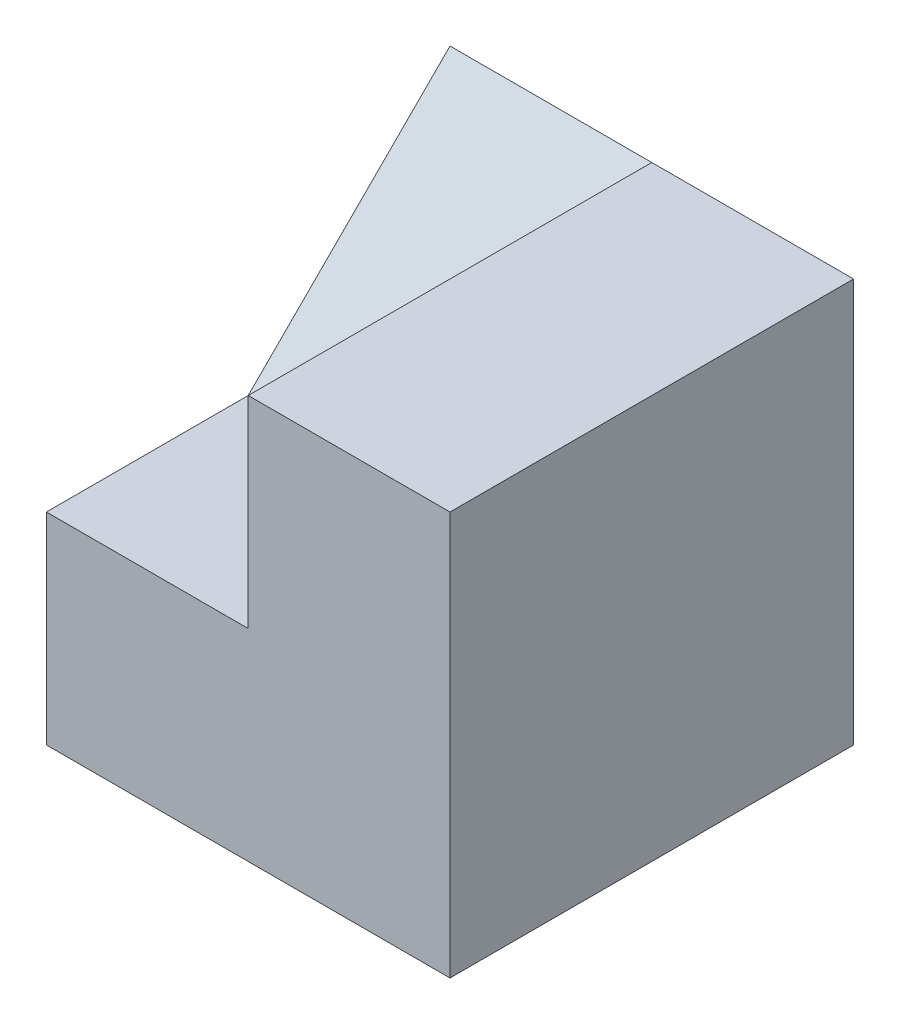
SolidWorks part; units mm, degrees
ref_plane "Front" through (0, 0, 0) normal (0, 0, 1) x (1, 0, 0)
ref_plane "Top" through (0, 0, 0) normal (0, 1, 0) x (1, 0, 0)
ref_plane "Right" through (0, 0, 0) normal (1, 0, 0) x (0, 0, -1)
sketch "Sketch1" plane through (0, 0, 0) normal (0, 1, 0) x (1, 0, 0)
  line L1 (-2, -2) -> (2, -2)
  line L2 (-2, -2) -> (-2, 2)
  line L3 (-2, 2) -> (2, 2)
  line L4 (2, -2) -> (2, 2)
  line L5 (-2, -2) -> (2, 2) construction
  line L6 (-2, 2) -> (2, -2) construction
  point P0 (0, 0)
  dimension "D1" = 4
  dimension "D2" = 4
extrude "Boss-Extrude1" add sketch "Sketch1" along normal blind 4
sketch "Sketch2" plane through (-2, 0, 0) normal (-1, 0, 0) x (0, 0, 1)
  line L5 (0, 2) -> (2, 2)
  line L6 (-2, 4) -> (0, 2)
  line L9 (-2, 0) -> (2, 0)
  line L10 (2, 0) -> (2, 4)
  line L11 (2, 4) -> (-2, 4)
  line L12 (-2, 4) -> (-2, 0)
  line L13 (-2, 0) -> (2, 0)
  line L14 (2, 0) -> (2, 4)
  line L15 (2, 4) -> (-2, 4)
  line L16 (-2, 4) -> (-2, 0)
  line M6 (2, 0) -> (2, 4)
  line M7 (2, 4) -> (-2, 4)
  dimension "D1" = 0
extrude "Cut-Extrude1" cut sketch "Sketch2" against normal blind 2 contours L6 L5 M7 M6 | L13 L14 L15 L16
